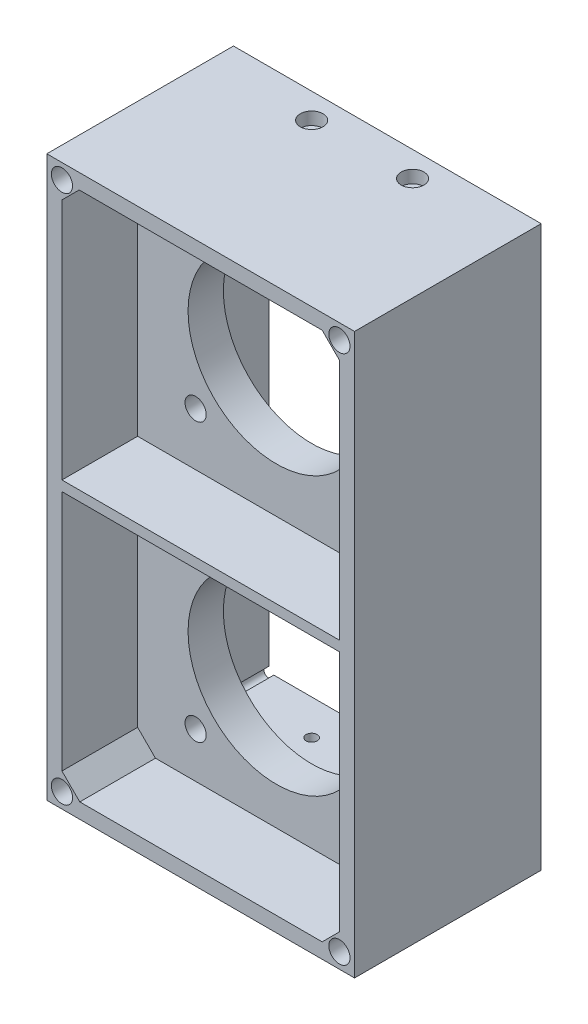
SolidWorks part; units mm, degrees
ref_plane "Front Plane" through (0, 0, 0) normal (0, 0, 1) x (1, 0, 0)
ref_plane "Top Plane" through (0, 0, 0) normal (0, 1, 0) x (1, 0, 0)
ref_plane "Right Plane" through (0, 0, 0) normal (1, 0, 0) x (0, 0, -1)
sketch "Sketch1" plane through (0, 0, 0) normal (0, 0, 1) x (1, 0, 0)
  line L1 (0, 0) -> (61, 0)
  line L2 (0, 0) -> (0, 111)
  line L3 (0, 111) -> (61, 111)
  line L4 (61, 0) -> (61, 111)
  line L5 (5, 5) -> (56, 5)
  line L6 (5, 5) -> (5, 106)
  line L7 (5, 106) -> (56, 106)
  line L8 (56, 5) -> (56, 106)
  dimension "D1" = 51
  dimension "D2" = 101
  dimension "D3" = 5
  dimension "D4" = 5
  dimension "D5" = 5
  dimension "D6" = 5
extrude "Boss-Extrude1" add sketch "Sketch1" along normal blind 15
sketch "Sketch2" plane through (0, 0, 15) normal (0, 0, 1) x (1, 0, 0)
  line L1 (0, 111) -> (61, 111)
  line L2 (0, 111) -> (0, 0)
  line L3 (0, 0) -> (61, 0)
  line L4 (61, 111) -> (61, 0)
extrude "Boss-Extrude2" add sketch "Sketch2" along normal blind 7
sketch "Sketch3" plane through (0, 0, 22) normal (0, 0, 1) x (1, 0, 0)
  line L0 (30.5, 111) -> (30.5, 0) construction
  line L1 (61, 111) -> (0, 111) construction
  line L2 (0, 0) -> (61, 0) construction
  line L4 (14.5, 67) -> (46.5, 67)
  line L5 (14.5, 67) -> (14.5, 99)
  line L6 (14.5, 99) -> (46.5, 99)
  line L7 (46.5, 67) -> (46.5, 99)
  line L8 (14.5, 67) -> (46.5, 99) construction
  line L9 (14.5, 99) -> (46.5, 67) construction
  line L10 (14.5, 12) -> (46.5, 12)
  line L11 (14.5, 12) -> (14.5, 44)
  line L12 (14.5, 44) -> (46.5, 44)
  line L13 (46.5, 12) -> (46.5, 44)
  line L14 (14.5, 12) -> (46.5, 44) construction
  line L15 (14.5, 44) -> (46.5, 12) construction
  circle A0 centre (30.5, 83) radius 17.5
  circle A1 centre (30.5, 28) radius 17.5
  circle A2 centre (46.5, 99) radius 1.75
  circle A3 centre (14.5, 99) radius 1.75
  circle A4 centre (46.5, 67) radius 1.75
  circle A5 centre (14.5, 67) radius 1.75
  circle A6 centre (14.5, 44) radius 1.75
  circle A7 centre (46.5, 44) radius 1.75
  circle A8 centre (46.5, 12) radius 1.75
  circle A9 centre (14.5, 12) radius 1.75
  point P10 (30.5, 55.5)
  dimension "D1" = 35
  dimension "D3" = 27.5
  dimension "D5" = 3.5
  dimension "D2" = 55
  dimension "D4" = 32
extrude "Cut-Extrude1" cut sketch "Sketch3" against normal through all contours A0 | A1 | L10 A8 L13 | L13 A8 L10 | A2 | A3 | A5 | A4 | A7 | A6 | A9
sketch "Sketch4" plane through (0, 0, 22) normal (0, 0, 1) x (1, 0, 0)
  circle A0 centre (14.5, 99) radius 2.1
  circle A1 centre (46.5, 99) radius 2.1
  circle A2 centre (46.5, 67) radius 2.1
  circle A3 centre (46.5, 44) radius 2.1
  circle A4 centre (14.5, 67) radius 2.1
  circle A5 centre (14.5, 44) radius 2.1
  circle A6 centre (14.5, 12) radius 2.1
  circle A7 centre (46.5, 12) radius 2.1
  dimension "D1" = 4.2
extrude "Cut-Extrude2" cut sketch "Sketch4" against normal blind 5
sketch "Sketch5" plane through (0, 0, 0) normal (0, 0, -1) x (-1, 0, 0)
  line L0 (-56, 106) -> (-5, 106) construction
  line L1 (-58, 3) -> (-3, 3)
  line L2 (-58, 3) -> (-58, 108)
  line L3 (-58, 108) -> (-3, 108)
  line L4 (-3, 3) -> (-3, 108)
  line L5 (-58, 3) -> (-3, 108) construction
  line L6 (-58, 108) -> (-3, 3) construction
  line L7 (-5, 106) -> (-5, 5) construction
  line L8 (-56, 5) -> (-56, 106) construction
  line L9 (-5, 5) -> (-56, 5) construction
  line L11 (-56, 106) -> (-5, 106)
  line L12 (-56, 106) -> (-56, 5)
  line L13 (-56, 5) -> (-5, 5)
  line L14 (-5, 106) -> (-5, 5)
  point P0 (-30.5, 55.5)
  dimension "D1" = 2
  dimension "D2" = 2
  dimension "D3" = 2
  dimension "D4" = 2
extrude "Boss-Extrude3" add sketch "Sketch5" along normal blind 2
fillet "Fillet1" radius 1
sketch "Sketch6" plane through (0, 0, 0) normal (0, -1, 0) x (-1, 0, 0)
  line L0 (0, -5) -> (-61, -5) construction
  line L1 (0, -22) -> (0, 0) construction
  line L2 (-61, -22) -> (-61, 0) construction
  line L3 (0, 0) -> (-61, 0) construction
  circle A0 centre (-20.5, -5) radius 1.1
  circle A1 centre (-40.5, -5) radius 1.1
  point P8 (-30.5, -5)
  dimension "D4" = 2.2
  dimension "D1" = 5
  dimension "D2" = 10
  dimension "D3" = 10
extrude "Cut-Extrude3" cut sketch "Sketch6" against normal through all
sketch "Sketch7" plane through (0, 0, 0) normal (0, -1, 0) x (1, 0, 0)
  circle A0 centre (20.5, 5) radius 2.25
  circle A1 centre (40.5, 5) radius 2.25
  dimension "D1" = 4.5
extrude "Cut-Extrude4" cut sketch "Sketch7" against normal blind 2.5
sketch "Sketch8" plane through (0, 111, 0) normal (0, 1, 0) x (1, 0, 0)
  circle A0 centre (40.5, -5) radius 2.25
  circle A1 centre (20.5, -5) radius 2.25
  dimension "D1" = 4.5
extrude "Cut-Extrude5" cut sketch "Sketch8" against normal blind 2.5
sketch "Sketch9" plane through (0, 0, -2) normal (0, 0, -1) x (-1, 0, 0)
  line L0 (-56, 106) -> (-56, 5) construction
  circle A0 centre (-56, 106) radius 1
  circle A1 centre (-5, 106) radius 1
  circle A2 centre (-5, 5) radius 1
  circle A3 centre (-56, 5) radius 1
  dimension "D1" = 2
extrude "Cut-Extrude6" cut sketch "Sketch9" against normal up to surface (17 mm away)
sketch "Sketch10" plane through (0, 0, 22) normal (0, 0, 1) x (1, 0, 0)
  line L0 (6.5355, 3) -> (3, 6.5355)
  line L1 (0, 0) -> (61, 0)
  line L2 (0, 0) -> (0, 111)
  line L3 (0, 111) -> (61, 111)
  line L4 (61, 0) -> (61, 111)
  line L5 (3, 3) -> (58, 3)
  line L6 (3, 3) -> (3, 108)
  line L7 (3, 108) -> (58, 108)
  line L8 (58, 3) -> (58, 108)
  line L9 (3, 104.5805) -> (6.4195, 108)
  line L10 (54.5805, 3) -> (58, 6.4195)
  line L11 (54.5805, 108) -> (58, 104.5805)
  line L13 (3, 54.5) -> (58, 54.5)
  line L14 (3, 54.5) -> (3, 56.5)
  line L15 (3, 56.5) -> (58, 56.5)
  line L16 (58, 54.5) -> (58, 56.5)
  line M19 (0, 111) -> (0, 0)
  line M20 (0, 0) -> (61, 0)
  line M21 (61, 0) -> (61, 111)
  line M22 (61, 111) -> (0, 111)
  dimension "D1" = 3
  dimension "D2" = 3
  dimension "D3" = 3
  dimension "D4" = 3
  dimension "D5" = 5
  dimension "D6" = 45
  dimension "D7" = 45
  dimension "D8" = 2
  dimension "D9" = 51.5
extrude "Boss-Extrude4" add sketch "Sketch10" along normal blind 15 contours L8 L5 L6 L7 M22 M19 M20 M21 | L6 L5 L0 | L6 L9 L7 | L7 L11 L8 | L10 L5 L8 | L14 L13 L16 L15
sketch "Sketch11" plane through (0, 0, 37) normal (0, 0, 1) x (1, 0, 0)
  line L0 (0, 0) -> (61, 0) construction
  line L1 (3, 3) -> (58, 3)
  line L2 (3, 3) -> (3, 108)
  line L3 (3, 108) -> (58, 108)
  line L4 (58, 3) -> (58, 108)
  line L5 (0, 111) -> (0, 0) construction
  line L6 (61, 111) -> (0, 111) construction
  line L7 (61, 0) -> (61, 111) construction
  circle A0 centre (3, 3) radius 2.1
  circle A1 centre (3, 108) radius 2.1
  circle A2 centre (58, 108) radius 2.1
  circle A3 centre (58, 3) radius 2.1
  dimension "D5" = 4.2
  dimension "D1" = 3
  dimension "D2" = 3
  dimension "D3" = 3
  dimension "D4" = 3
extrude "Cut-Extrude7" cut sketch "Sketch11" against normal blind 6 contours A0 | A1 | A2 | A3
